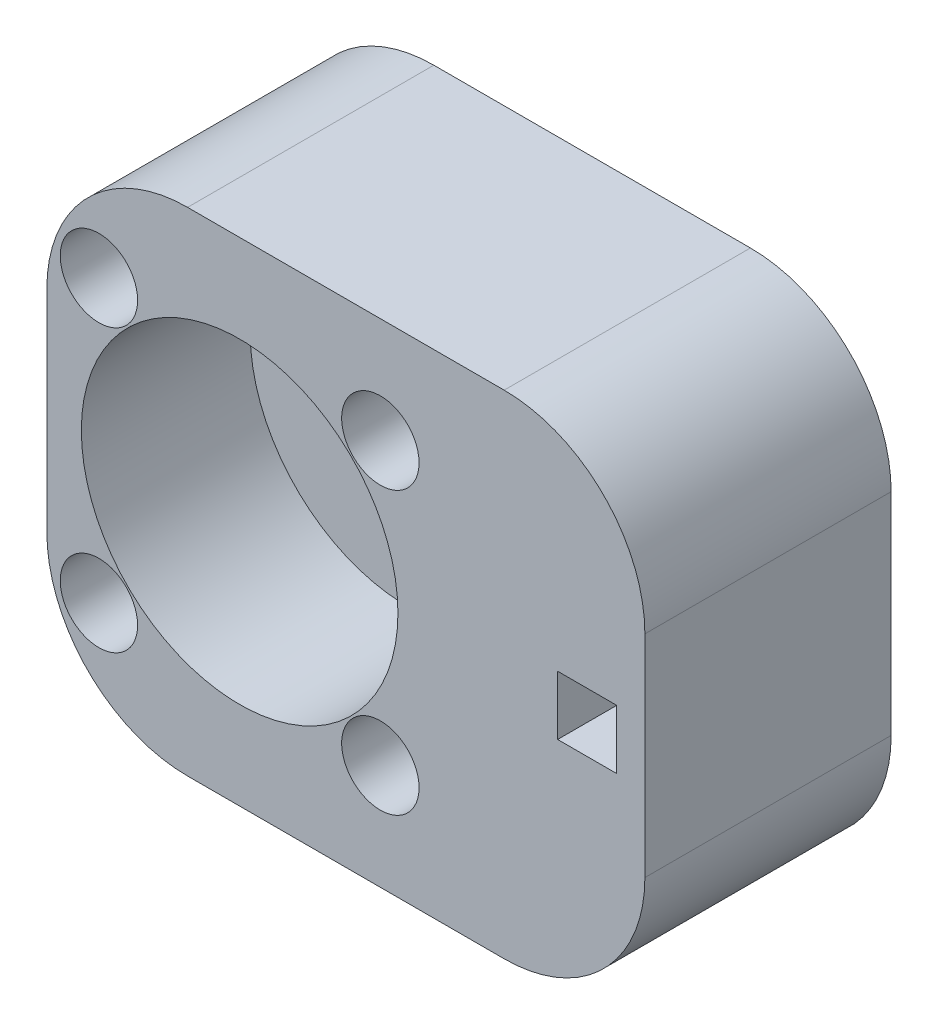
SolidWorks part; units mm, degrees
ref_plane "Front Plane" through (0, 0, 0) normal (0, 0, 1) x (1, 0, 0)
ref_plane "Top Plane" through (0, 0, 0) normal (0, 1, 0) x (1, 0, 0)
ref_plane "Right Plane" through (0, 0, 0) normal (1, 0, 0) x (0, 0, -1)
sketch "Sketch1" plane through (0, 0, 0) normal (0, 0, 1) x (1, 0, 0)
  line L0 (-118.1513, -31.2203) -> (865.6513, -31.2203) construction
  line L1 (358.75, -74.1782) -> (358.75, -119.5782) construction
  line L4 (401.25, -114.3782) -> (358.75, -114.3782)
  line L5 (401.25, -114.3782) -> (401.25, -79.3782)
  line L6 (401.25, -79.3782) -> (358.75, -79.3782)
  line L7 (358.75, -114.3782) -> (358.75, -79.3782)
  point P4 (358.75, -96.8782)
  point P5 (358.75, -96.8782)
  point P6 (373.75, -31.2203)
  dimension "D1" = 42.5
  dimension "D2" = 15
  dimension "D3" = 35
extrude "Boss-Extrude1" add sketch "Sketch1" along normal blind 17.5 contours L6 L7 L4 L5
sketch "Sketch3" plane through (0, 0, 17.5) normal (0, 0, 1) x (1, 0, 0)
  line L0 (401.25, -96.8782) -> (6.1928, -96.8782) construction
  line L1 (401.25, -114.3782) -> (401.25, -79.3782) construction
  line L3 (399.25, -98.9782) -> (395.05, -98.9782)
  line L4 (399.25, -98.9782) -> (399.25, -94.7782)
  line L5 (399.25, -94.7782) -> (395.05, -94.7782)
  line L6 (395.05, -98.9782) -> (395.05, -94.7782)
  line L7 (399.25, -98.9782) -> (395.05, -94.7782) construction
  line L8 (399.25, -94.7782) -> (395.05, -98.9782) construction
  point P4 (397.15, -96.8782)
  dimension "D1" = 4.2
  dimension "D2" = 2
extrude "Cut-Extrude1" cut sketch "Sketch3" against normal offset from surface (12.5 mm away) 5 up to face at (380, -96.8782, 0)
sketch "Sketch4" plane through (0, 0, 17.5) normal (0, 0, 1) x (1, 0, 0)
  circle A8 centre (382.45, -86.8782) radius 1.6 construction
  circle A9 centre (382.45, -106.8782) radius 1.6 construction
  circle A10 centre (362.45, -86.8782) radius 1.6 construction
  circle A11 centre (362.45, -106.8782) radius 1.6 construction
  circle A12 centre (382.45, -86.8782) radius 1.6
  circle A13 centre (382.45, -106.8782) radius 1.6
  circle A14 centre (362.45, -86.8782) radius 1.6
  circle A15 centre (362.45, -106.8782) radius 1.6
extrude "Cut-Extrude2" cut sketch "Sketch4" against normal through all
sketch "Sketch5" plane through (0, 0, 17.5) normal (0, 0, 1) x (1, 0, 0)
  circle A0 centre (382.45, -106.8782) radius 2.75
  circle A1 centre (382.45, -86.8782) radius 2.75
  circle A2 centre (362.45, -86.8782) radius 2.75
  circle A3 centre (362.45, -106.8782) radius 2.75
  dimension "D1" = 5.5
extrude "Cut-Extrude3" cut sketch "Sketch5" against normal offset from surface (15 mm away) 2.5 up to face at (384.05, -106.8782, 0)
sketch "Sketch6" plane through (0, 0, 17.5) normal (0, 0, 1) x (1, 0, 0)
  line L0 (386.15, -74.1782) -> (358.75, -74.1782) construction
  line L2 (386.15, -74.1782) -> (358.75, -74.1782) construction
  line L8 (362.45, -86.8782) -> (382.45, -106.8782) construction
  line L9 (362.45, -106.8782) -> (382.45, -86.8782) construction
  circle A0 centre (372.45, -96.8782) radius 11.25
  dimension "D1" = 22.5
extrude "Cut-Extrude4" cut sketch "Sketch6" against normal blind 12
fillet "Fillet1" radius 10 4 edges at (358.75, -79.3782, 8.75) (358.75, -114.3782, 8.75) (401.25, -114.3782, 8.75) (401.25, -79.3782, 8.75)
